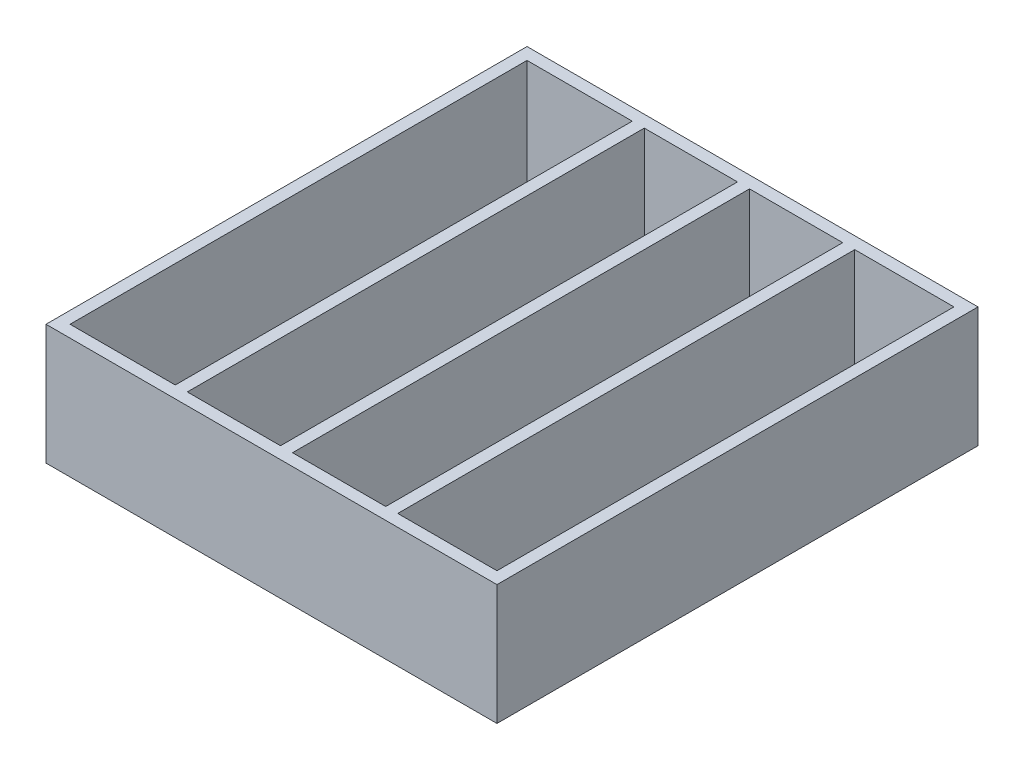
SolidWorks part; units mm, degrees
ref_plane "Front Plane" through (0, 0, 0) normal (0, 0, 1) x (1, 0, 0)
ref_plane "Top Plane" through (0, 0, 0) normal (0, 1, 0) x (1, 0, 0)
ref_plane "Right Plane" through (0, 0, 0) normal (1, 0, 0) x (0, 0, -1)
sketch "Sketch2" plane through (0, 0, 0) normal (0, 1, 0) x (1, 0, 0)
  line L0 (-18, 38) -> (-18, -38)
  line L1 (-37.5, -40) -> (37.5, -40)
  line L2 (-37.5, -40) -> (-37.5, 40)
  line L3 (-37.5, 40) -> (37.5, 40)
  line L4 (37.5, -40) -> (37.5, 40)
  line L5 (-35.5, -38) -> (-18, -38)
  line L6 (-35.5, -38) -> (-35.5, 38)
  line L7 (-35.5, 38) -> (-18, 38)
  line L8 (35.5, -38) -> (35.5, 38)
  line L9 (-16, 38) -> (-16, -38)
  line L10 (-0.5, 38) -> (-0.5, -38)
  line L11 (1.5, 38) -> (1.5, -38)
  line L12 (17, 38) -> (17, -38)
  line L13 (19, 38) -> (19, -38)
  line L14 (-16, 38) -> (-0.5, 38)
  line L15 (1.5, 38) -> (17, 38)
  line L16 (19, 38) -> (35.5, 38)
  line L17 (19, -38) -> (35.5, -38)
  line L18 (1.5, -38) -> (17, -38)
  line L19 (-16, -38) -> (-0.5, -38)
  point P0 (0, 0)
  point P6 (0, 0)
  dimension "D1" = 75
  dimension "D2" = 80
  dimension "D3" = 37.5
  dimension "D4" = 40
  dimension "D5" = 71
  dimension "D6" = 76
  dimension "D7" = 2
  dimension "D8" = 2
  dimension "D9" = 2
  dimension "D10" = 17.5
  dimension "D11" = 3
extrude "Boss-Extrude1" add sketch "Sketch2" along normal blind 18
sketch "Sketch3" plane through (0, 0, 0) normal (0, -1, 0) x (1, 0, 0)
  line L0 (-0.5, 38) -> (-0.5, -38) construction
  line L6 (37.5, -40) -> (-37.5, -40)
  line L7 (37.5, -40) -> (37.5, 40)
  line L8 (37.5, 40) -> (-37.5, 40)
  line L9 (-37.5, -40) -> (-37.5, 40)
  point P0 (-0.5, 0)
  point P1 (-0.5, 0)
extrude "Boss-Extrude3" add sketch "Sketch3" along normal blind 2
sketch "Sketch4" plane through (0, 0, 0) normal (0, 1, 0) x (1, 0, 0)
  line L4 (-18, -38) -> (-18, 38)
  line L5 (-18, 38) -> (-35.5, 38)
  line L6 (-35.5, 38) -> (-35.5, -38)
  line L7 (-35.5, -38) -> (-18, -38)
  line L8 (-18, -38) -> (-18, 38)
  line L9 (-18, 38) -> (-35.5, 38)
  line L10 (-35.5, 38) -> (-35.5, -38)
  line L11 (-35.5, -38) -> (-18, -38)
  circle A0 centre (-26.75, -0.5) radius 1.5
  dimension "D3" = 8.75
  dimension "D4" = 3
  dimension "D2" = 37.5
  dimension "D1" = 0
extrude "Cut-Extrude1" cut sketch "Sketch4" against normal through all contours A0
mirror "Mirror1" about plane through (0, 0, 0) normal (1, 0, 0) of "Cut-Extrude1"
